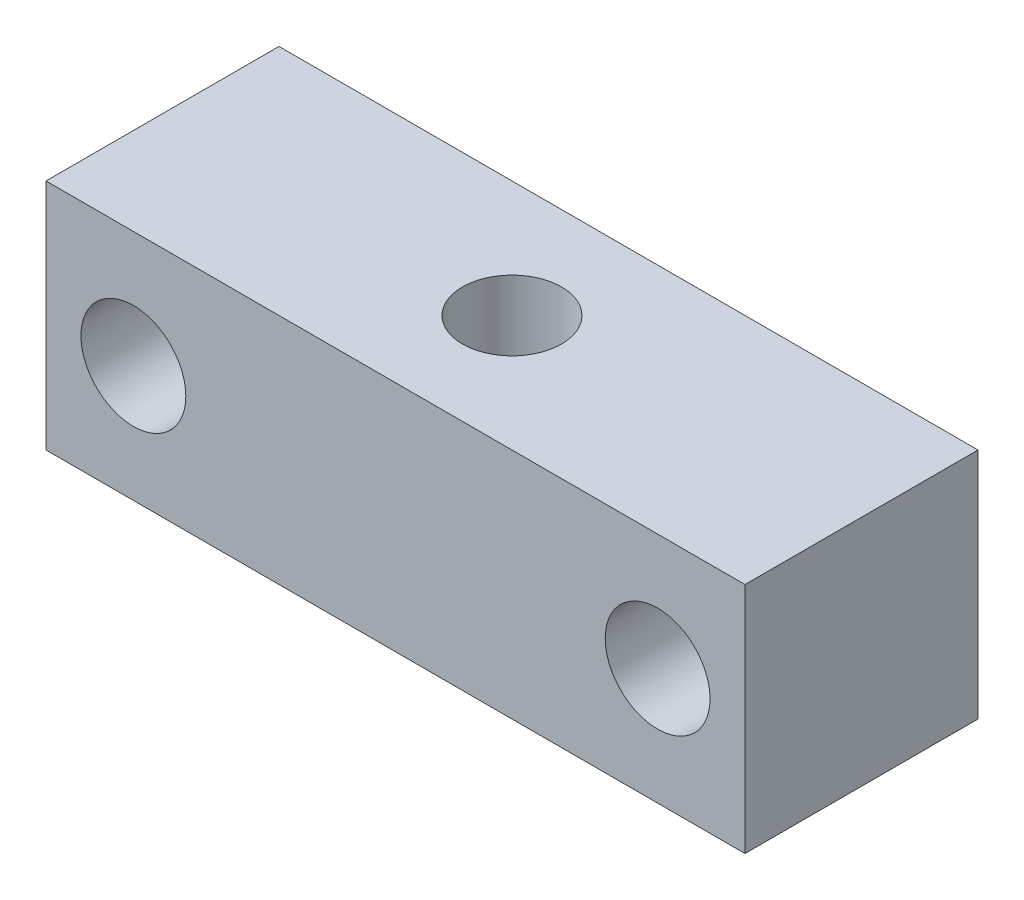
SolidWorks part; units mm, degrees
ref_plane "前视基准面" through (0, 0, 0) normal (0, 0, 1) x (1, 0, 0)
ref_plane "上视基准面" through (0, 0, 0) normal (0, 1, 0) x (1, 0, 0)
ref_plane "右视基准面" through (0, 0, 0) normal (1, 0, 0) x (0, 0, -1)
sketch "草图1" plane through (0, 0, 0) normal (0, 0, 1) x (1, 0, 0)
  line L0 (0, 0) -> (0, 23.9514) construction
  line L1 (-30, 10) -> (30, 10)
  line L2 (-30, 10) -> (-30, -10)
  line L3 (-30, -10) -> (30, -10)
  line L4 (30, 10) -> (30, -10)
  line L5 (-30, 10) -> (30, -10) construction
  line L6 (-30, -10) -> (30, 10) construction
  circle A0 centre (-22.5, 0) radius 4.5
  circle A1 centre (22.5, 0) radius 4.5
  point P0 (0, 0)
  dimension "D3" = 9
  dimension "D1" = 60
  dimension "D2" = 20
  dimension "D4" = 45
  dimension "D5" = 10
extrude "凸台-拉伸1" add sketch "草图1" along normal blind 20
hole_wizard "M10 螺纹孔1" positions "3D草图1" profile "草图2" tap size "M10" standard "GB"
sketch3d "3D草图1"
  line L0 (30, 10, 0) -> (-30, 10, 0) construction
  line L1 (30, 10, 20) -> (30, 10, 0) construction
  point P0 (0, 10, 10)
  dimension "D1" = 10
  dimension "D2" = 30
sketch "草图2" plane through (0, 10, 10) normal (1, 0, 0) x (0, 0, 1)
  line L0 (0, 0) -> (0, 27.0537)
  line L1 (0, 27.0537) -> (4.25, 24.5)
  line L2 (4.25, 24.5) -> (4.25, 0)
  line L5 (4.25, 0) -> (0, 0)
  line L10 (0, 27.0537) -> (-4.25, 24.5) construction
  line L11 (0, -6.35) -> (0, 107.95) construction
  dimension "螺纹孔钻头直径" = 8.5
  dimension "螺纹孔钻头深度" = 24.5
  dimension "导头角度" = 118
cosmetic thread "孔螺蚊线1" parameters "D1"=20, "D2"=10
